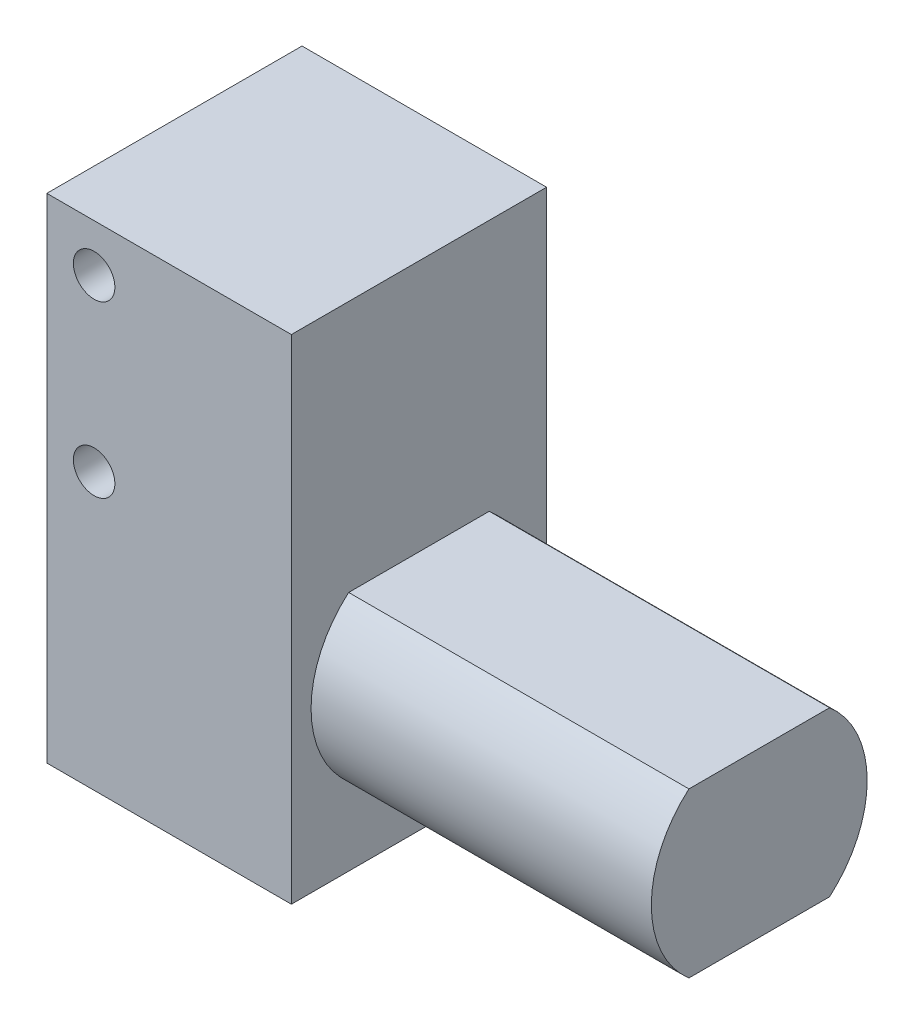
SolidWorks part; units mm, degrees
ref_plane "Front Plane" through (0, 0, 0) normal (0, 0, 1) x (1, 0, 0)
ref_plane "Top Plane" through (0, 0, 0) normal (0, 1, 0) x (1, 0, 0)
ref_plane "Right Plane" through (0, 0, 0) normal (1, 0, 0) x (0, 0, -1)
sketch "Sketch1" plane through (0, 0, 0) normal (0, 0, 1) x (1, 0, 0)
  line L1 (0, 0) -> (23, 0)
  line L2 (0, 0) -> (0, 46.4)
  line L3 (0, 46.4) -> (23, 46.4)
  line L4 (23, 0) -> (23, 46.4)
  dimension "D1" = 23
  dimension "D2" = 46.4
extrude "Boss-Extrude1" add sketch "Sketch1" along normal mid plane 24
sketch "Sketch6" plane through (0, 0, 12) normal (0, 0, 1) x (1, 0, 0)
  line L0 (23, 46.4) -> (0, 46.4) construction
  line L1 (11.5, 46.4) -> (11.5, 0) construction
  line L2 (0, 46.4) -> (0, 0) construction
  line L3 (0, 0) -> (23, 0) construction
  circle A0 centre (4.45, 41.95) radius 1.95
  circle A1 centre (4.45, 25.95) radius 1.95
  dimension "D1" = 3.9
  dimension "D2" = 2.5
  dimension "D3" = 2.5
  dimension "D4" = 16
  dimension "D5" = 14.1
extrude "Cut-Extrude1" cut sketch "Sketch6" against normal blind 5.5
mirror "Mirror1" about plane through (0, 0, 0) normal (0, 0, 1) of "Cut-Extrude1"
sketch "Sketch7" plane through (0, 0, 0) normal (-1, 0, 0) x (0, 0, 1)
  line L1 (12, 46.4) -> (-12, 46.4) construction
  circle A0 centre (0, 34.2) radius 2.7
  dimension "D1" = 5.4
  dimension "D2" = 9.5
  dimension "D3" = 14.9
extrude "Boss-Extrude2" add sketch "Sketch7" along normal blind 9
sketch "Sketch8" plane through (0, 0, 0) normal (0, 1, 0) x (1, 0, 0)
  line L0 (-9, 2.7) -> (-9, -2.7) construction
  line L1 (-9, 1.75) -> (-2, 1.75)
  line L2 (-9, 1.75) -> (-9, 2.7)
  line L3 (-9, 2.7) -> (-2, 2.7)
  line L4 (-2, 1.75) -> (-2, 2.7)
  line L7 (-9, -1.75) -> (-2, -1.75)
  line L8 (-9, -1.75) -> (-9, -2.7)
  line L9 (-9, -2.7) -> (-2, -2.7)
  line L10 (-2, -1.75) -> (-2, -2.7)
  line L13 (-9, -2.7) -> (0, -2.7) construction
  line L14 (0, 2.7) -> (-9, 2.7) construction
  dimension "D1" = 3.5
  dimension "D2" = 7
extrude "Cut-Extrude2" cut sketch "Sketch8" along normal through all
sketch "Sketch9" plane through (0, 0, 0) normal (-1, 0, 0) x (0, 0, 1)
  line L0 (0, -1000) -> (0, 49000) construction
  line L3 (12, 0) -> (-12, 0) construction
  circle A0 centre (-8, 10.45) radius 1.95
  circle A1 centre (8, 10.45) radius 1.95
  dimension "D1" = 3.9
  dimension "D3" = 8.5
  dimension "D2" = 16
extrude "Cut-Extrude3" cut sketch "Sketch9" against normal blind 5.5
sketch "Sketch10" plane through (23, 0, 0) normal (1, 0, 0) x (0, 0, -1)
  line L0 (-12, 0) -> (12, 0) construction
  circle A0 centre (0, 15) radius 10.15
  dimension "D1" = 15
  dimension "D2" = 20.3
extrude "Boss-Extrude3" add sketch "Sketch10" along normal blind 32
sketch "Sketch11" plane through (0, 0, 0) normal (0, 0, 1) x (1, 0, 0)
  line L0 (23, 0) -> (23, 46.4) construction
  line L1 (55, 25.15) -> (23, 25.15)
  line L2 (55, 25.15) -> (55, 22.7)
  line L3 (55, 22.7) -> (23, 22.7)
  line L4 (23, 25.15) -> (23, 22.7)
  line L5 (23, 4.85) -> (23, 25.15) construction
  line L6 (55, 4.85) -> (23, 4.85)
  line L7 (55, 4.85) -> (55, 7.3)
  line L8 (55, 7.3) -> (23, 7.3)
  line L9 (23, 4.85) -> (23, 7.3)
  dimension "D1" = 15.4
extrude "Cut-Extrude4" cut sketch "Sketch11" against normal through all both and the other way through all
sketch "Sketch12" plane through (0, 0, 0) normal (0, -1, 0) x (1, 0, 0)
  line L0 (23, 12) -> (23, -12) construction
  line L1 (13, 4.5) -> (16, 4.5)
  line L2 (13, 4.5) -> (13, -4.5)
  line L3 (13, -4.5) -> (16, -4.5)
  line L4 (16, 4.5) -> (16, -4.5)
  point P4 (13, 0)
  dimension "D1" = 3
  dimension "D2" = 9
  dimension "D3" = 7
extrude "Cut-Extrude5" cut sketch "Sketch12" against normal blind 5
equation "\"width\"= 24"
equation "\"thk\"= 3"
equation "\"holesize\"= 4.2"
equation "\"holedistance\"= ( 20 + 12 ) / 2"
equation "\"threaded_hole\"= 3.9"
equation "\"D4@Sketch6\"=\"holedistance\""
equation "\"D1@Sketch6\"=\"threaded_hole\""
equation "\"D2@Sketch9\"=\"holedistance\""
equation "\"D1@Sketch9\"=\"threaded_hole\""
equation "\"fillet_radius\"= 2"
equation "\"ground_clearance\"= 25"
equation "\"tire_thk\"= 3"
equation "\"innerwheel_diam\" = \"wheel_diam\"-2*\"tire_thk\""
equation "\"innerwheel_thk\"= 8"
equation "\"wheel_diam\"= 2*(\"width\"/2+\"ground_clearance\")"
equation "\"coloursensor_holesize\"= 2.65"
equation "\"hole_to_edge\" = 4"
